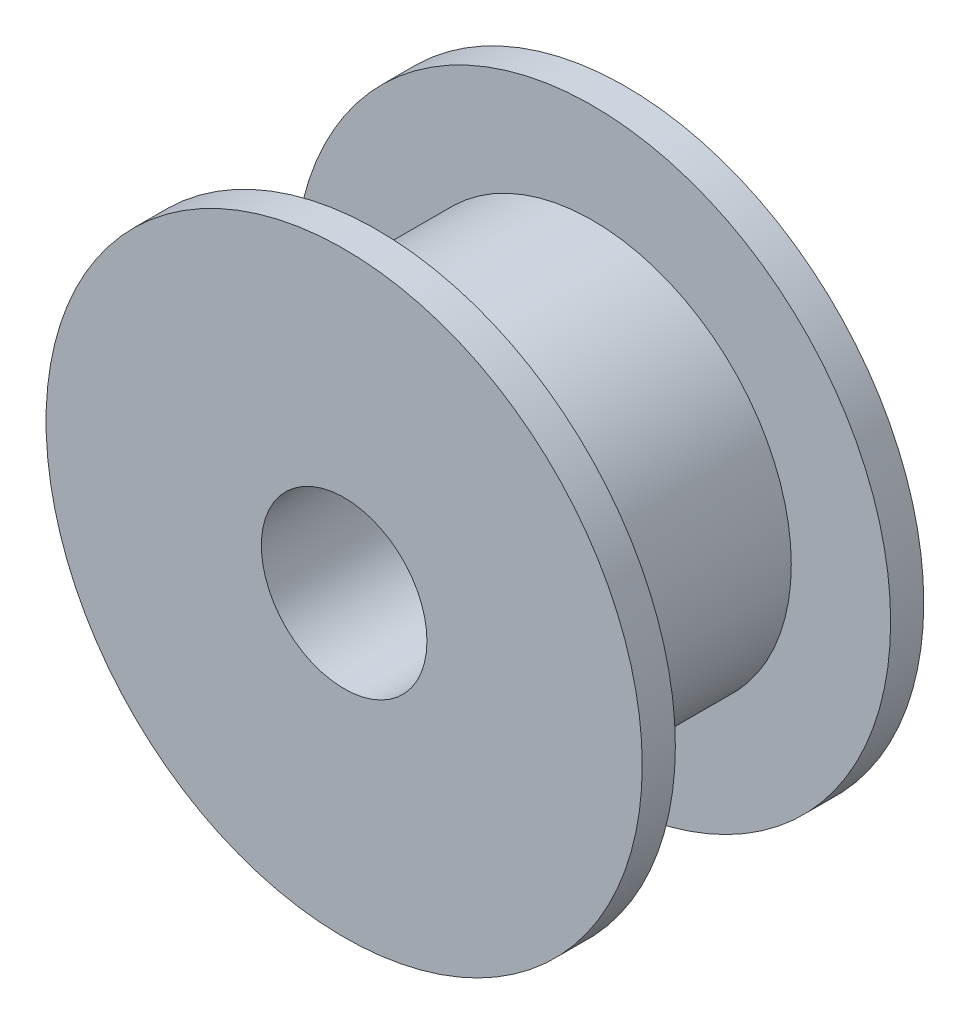
SolidWorks part; units mm, degrees
ref_plane "前视基准面" through (0, 0, 0) normal (0, 0, 1) x (1, 0, 0)
ref_plane "上视基准面" through (0, 0, 0) normal (0, 1, 0) x (1, 0, 0)
ref_plane "右视基准面" through (0, 0, 0) normal (1, 0, 0) x (0, 0, -1)
sketch "草图1" plane through (0, 0, 0) normal (0, 0, 1) x (1, 0, 0)
  circle A0 centre (0, 0) radius 9
  dimension "D1" = 18
extrude "凸台-拉伸1" add sketch "草图1" along normal blind 1
sketch "草图2" plane through (0, 0, 1) normal (0, 0, 1) x (1, 0, 0)
  circle A0 centre (0, 0) radius 6
  dimension "D1" = 12
extrude "凸台-拉伸2" add sketch "草图2" along normal blind 6.5
sketch "草图3" plane through (0, 0, 7.5) normal (0, 0, 1) x (1, 0, 0)
  circle A0 centre (0, 0) radius 9
  dimension "D1" = 18
extrude "凸台-拉伸3" add sketch "草图3" along normal blind 1
sketch "草图4" plane through (0, 0, 8.5) normal (0, 0, 1) x (1, 0, 0)
  circle A0 centre (0, 0) radius 2.5
  dimension "D1" = 5
extrude "切除-拉伸1" cut sketch "草图4" against normal through all
